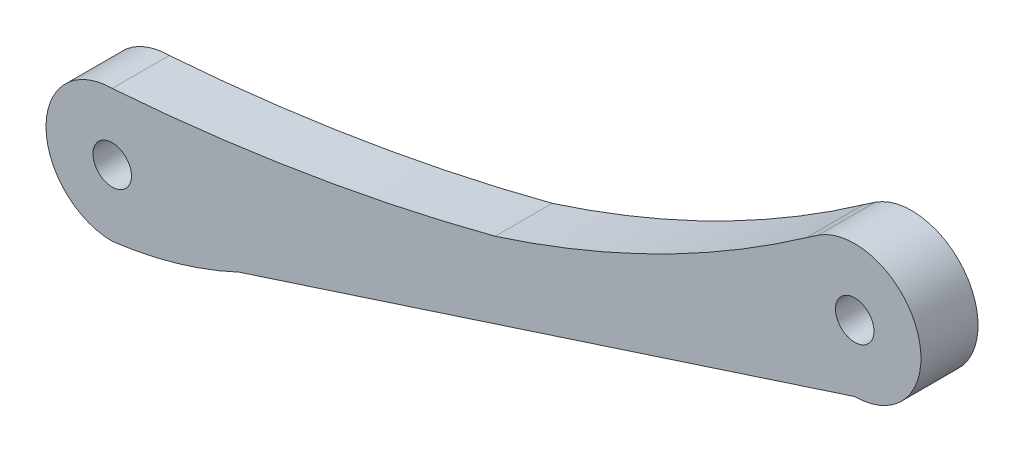
SolidWorks part; units mm, degrees
ref_plane "Front Plane" through (0, 0, 0) normal (0, 0, 1) x (1, 0, 0)
ref_plane "Top Plane" through (0, 0, 0) normal (0, 1, 0) x (1, 0, 0)
ref_plane "Right Plane" through (0, 0, 0) normal (1, 0, 0) x (0, 0, -1)
sketch "Sketch1" plane through (0, 0, 0) normal (0, 0, 1) x (1, 0, 0)
  line L1 (74.1564, 30.6771) -> (72.9384, 29.8474)
  line L2 (13.3235, -3.101) -> (78.02, 17.9272)
  arc A0 (78.02, 17.9272) -> (74.1564, 30.6771) centre (78.02, 24.8875) ccw
  circle A1 centre (0, 0) radius 2.023
  circle A2 centre (78.02, 24.8875) radius 2.024
  arc A3 (0, 6.9565) -> (0, -6.9565) centre (0, 0) ccw
  arc A6 (0, 6.9565) -> (40.2359, 13.6216) centre (-16.5, 231.3453) ccw
  arc A9 (0, -6.9565) -> (13.3235, -3.101) centre (-5.435, 36.7736) ccw
  arc A11 (40.2359, 13.6216) -> (72.9384, 29.8474) centre (3.5209, 128.6872) ccw
extrude "Boss-Extrude1" add sketch "Sketch1" along normal blind 6 contours A11 A6 A3 A9 L2 A0 L1 A2 A1
move or copy body "Body-Move/Copy1" bodies to move or copy 102
